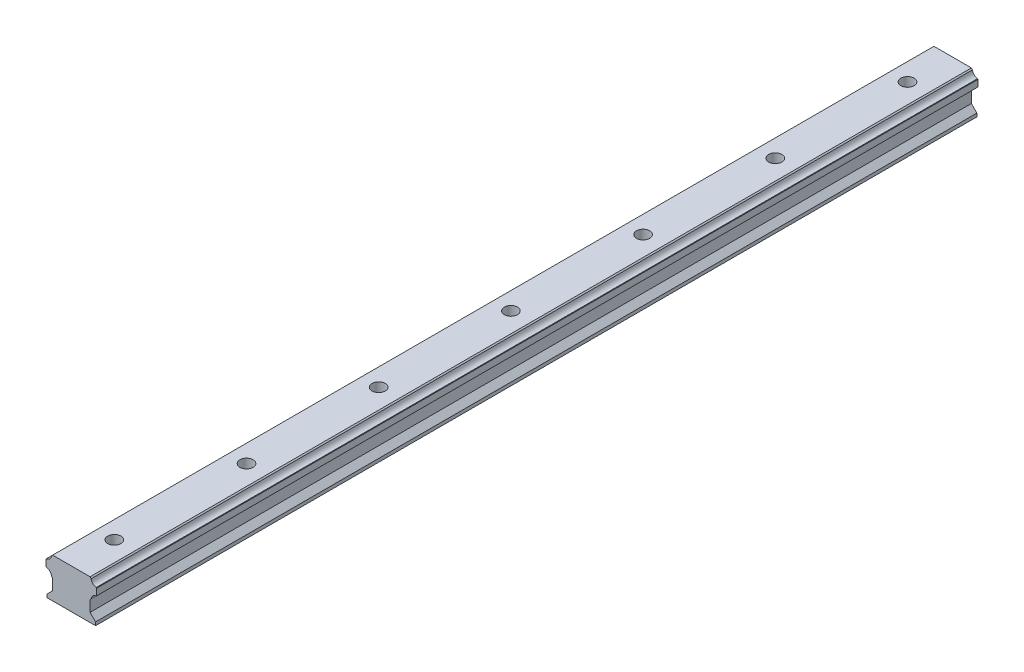
SolidWorks part; units mm, degrees
ref_plane "Piano frontale" through (0, 0, 0) normal (0, 0, 1) x (1, 0, 0)
ref_plane "Piano superiore" through (0, 0, 0) normal (0, 1, 0) x (1, 0, 0)
ref_plane "Piano destro" through (0, 0, 0) normal (1, 0, 0) x (0, 0, -1)
sketch "Schizzo1" plane through (0, 0, 0) normal (0, 0, 1) x (1, 0, 0)
  line L0 (-10.0012, -16.2762) -> (-7.5012, -13.7762)
  line L1 (-7.5012, -13.7762) -> (-7.5012, -8.7762)
  line L2 (-7.5012, -8.7762) -> (-8.0088, -8.2686)
  line L3 (-10.3066, -5.9708) -> (-10.5012, -5.7762)
  line L4 (-10.5012, -5.7762) -> (-10.5012, -2.7762)
  line L5 (-10.5012, -2.7762) -> (-10.3066, -2.5816)
  line L6 (-8.0088, -0.2838) -> (-7.5012, 0.2238)
  line L7 (-7.5012, 0.2238) -> (9.4988, 0.2238)
  line L8 (9.4988, 0.2238) -> (10.0064, -0.2838)
  line L9 (12.3042, -2.5816) -> (12.4988, -2.7762)
  line L10 (12.4988, -2.7762) -> (12.4988, -5.7762)
  line L11 (12.4988, -5.7762) -> (12.3042, -5.9708)
  line L12 (10.0064, -8.2686) -> (9.4988, -8.7762)
  line L13 (9.4988, -8.7762) -> (9.4988, -13.7762)
  line L14 (9.4988, -13.7762) -> (11.9988, -16.2762)
  line L17 (-10.0012, -16.2762) -> (-10.0012, -17.7762)
  line L18 (-10.0012, -17.7762) -> (11.9988, -17.7762)
  line L19 (11.9988, -17.7762) -> (11.9988, -16.2762)
  arc A0 (-8.0088, -8.2686) -> (-10.3066, -5.9708) centre (-10.5012, -8.4632) ccw
  arc A1 (-10.3066, -2.5816) -> (-8.0088, -0.2838) centre (-10.5012, -0.0892) ccw
  arc A2 (10.0064, -0.2838) -> (12.3042, -2.5816) centre (12.4988, -0.0892) ccw
  arc A3 (12.3042, -5.9708) -> (10.0064, -8.2686) centre (12.4988, -8.4632) ccw
  dimension "D1" = 17
  dimension "D2" = 18
extrude "Estrusione-Estrusione1" add sketch "Schizzo1" along normal blind 400
sketch "Schizzo2" plane through (0, 0.2238, 0) normal (0, 1, 0) x (1, 0, 0)
  line L0 (0.9988, -400) -> (0, 0) construction
  line L1 (9.4988, -400) -> (-7.5012, -400) construction
  line L2 (9.4988, -200) -> (-8.0088, -200) construction
  line L3 (9.4988, -400) -> (9.4988, 0) construction
  line L4 (-8.0088, -400) -> (-8.0088, 0) construction
  circle A0 centre (0.4994, -200) radius 3
  dimension "D1" = 6
extrude "Taglio-Estrusione1" cut sketch "Schizzo2" against normal through all
pattern_linear "Ripetizione a L1" count 4 spacing 60 along (0, 0, 1) of "Taglio-Estrusione1"
pattern_linear "Ripetizione a L2" count 4 spacing 60 along (0, 0, -1) of "Ripetizione a L1"
